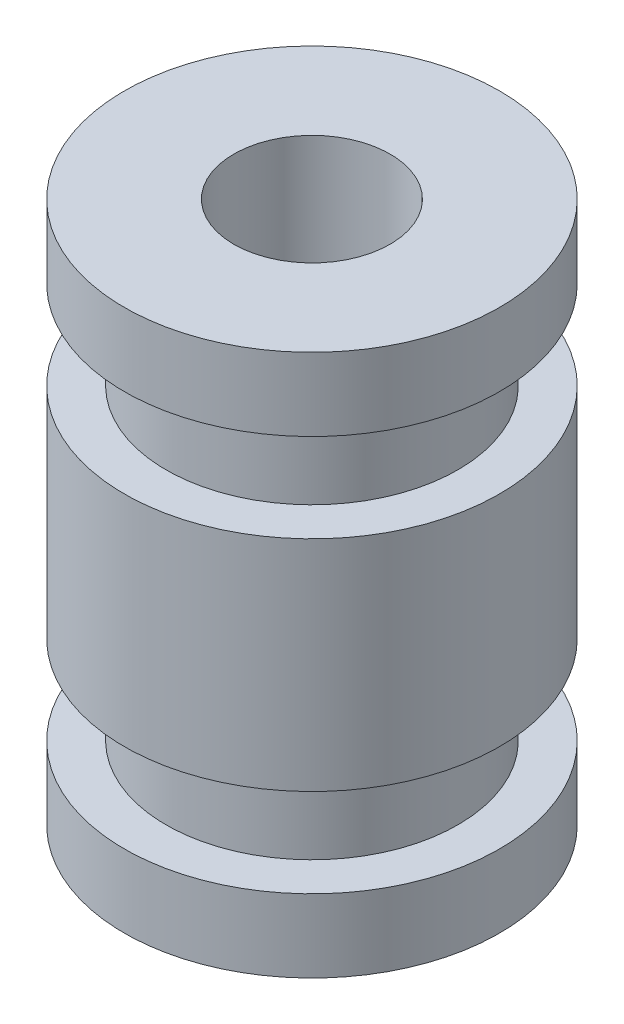
SolidWorks part; units mm, degrees
ref_plane "Front Plane" through (0, 0, 0) normal (0, 0, 1) x (1, 0, 0)
ref_plane "Top Plane" through (0, 0, 0) normal (0, 1, 0) x (1, 0, 0)
ref_plane "Right Plane" through (0, 0, 0) normal (1, 0, 0) x (0, 0, -1)
sketch "Sketch1" plane through (0, 0, 0) normal (0, 0, 1) x (1, 0, 0)
  line L0 (0, 0) -> (0, 13)
  line L1 (0, 13) -> (4.5, 13)
  line L2 (4.5, 13) -> (4.5, 11.25)
  line L3 (4.5, 11.25) -> (3.5, 11.25)
  line L4 (3.5, 11.25) -> (3.5, 9.125)
  line L5 (3.5, 9.125) -> (4.5, 9.125)
  line L6 (4.5, 9.125) -> (4.5, 3.875)
  line L7 (4.5, 3.875) -> (3.5, 3.875)
  line L8 (3.5, 3.875) -> (3.5, 1.75)
  line L9 (3.5, 1.75) -> (4.5, 1.75)
  line L10 (4.5, 1.75) -> (4.5, 0)
  line L11 (4.5, 0) -> (0, 0)
  dimension "D1" = 4.5
  dimension "D2" = 1.75
  dimension "D3" = 13
  dimension "D4" = 2.125
  dimension "D5" = 1
revolve "Revolve1" add sketch "Sketch1" angle 360 about L0
sketch "Sketch2" plane through (0, 13, 0) normal (0, 1, 0) x (1, 0, 0)
  circle A0 centre (0, 0) radius 1.875
  dimension "D1" = 3.75
extrude "Cut-Extrude1" cut sketch "Sketch2" against normal through all both and the other way through all
